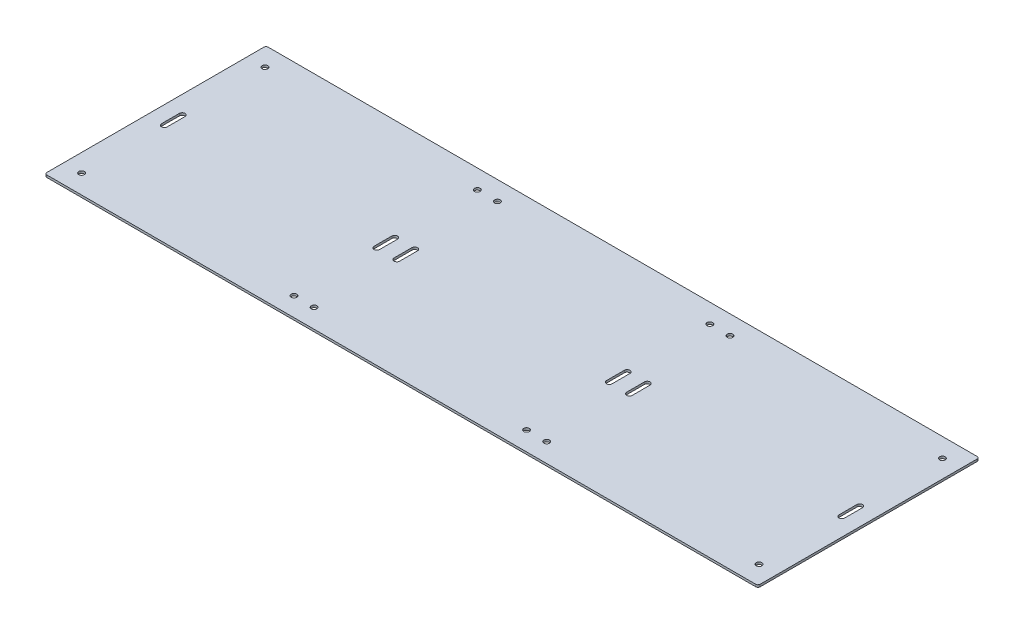
SolidWorks part; units mm, degrees
material "PC High Viscosity"
ref_plane "Front Plane" through (0, 0, 0) normal (0, 0, 1) x (1, 0, 0)
ref_plane "Top Plane" through (0, 0, 0) normal (0, 1, 0) x (1, 0, 0)
ref_plane "Right Plane" through (0, 0, 0) normal (1, 0, 0) x (0, 0, -1)
sketch "Sketch1" plane through (0, 0, 0) normal (0, 1, 0) x (1, 0, 0)
  line L0 (654.05, 574.675) -> (711.2, 574.675) construction
  line L1 (6.35, 0) -> (2019.3, 0)
  line L2 (0, 6.35) -> (0, 622.3)
  line L3 (6.35, 628.65) -> (2019.3, 628.65)
  line L4 (2025.65, 6.35) -> (2025.65, 622.3)
  line L5 (654.05, 574.675) -> (654.05, 53.975) construction
  line L6 (1371.6, 574.675) -> (1314.45, 574.675) construction
  line L7 (1371.6, 574.675) -> (1371.6, 53.975) construction
  line L8 (50.8, 339.725) -> (50.8, 288.925) construction
  line L9 (58.7375, 339.725) -> (58.7375, 288.925)
  line L10 (42.8625, 339.725) -> (42.8625, 288.925)
  line L11 (654.05, 339.725) -> (654.05, 288.925) construction
  line L12 (661.9875, 339.725) -> (661.9875, 288.925)
  line L13 (646.1125, 339.725) -> (646.1125, 288.925)
  line L14 (711.2, 339.725) -> (711.2, 288.925) construction
  line L15 (719.1375, 339.725) -> (719.1375, 288.925)
  line L16 (703.2625, 339.725) -> (703.2625, 288.925)
  line L17 (1012.825, 628.65) -> (1012.825, -49.4513) construction
  line L18 (1974.85, 339.725) -> (1974.85, 288.925) construction
  line L19 (1966.9125, 339.725) -> (1966.9125, 288.925)
  line L20 (1982.7875, 339.725) -> (1982.7875, 288.925)
  line L21 (1314.45, 339.725) -> (1314.45, 288.925) construction
  line L22 (1306.5125, 339.725) -> (1306.5125, 288.925)
  line L23 (1322.3875, 339.725) -> (1322.3875, 288.925)
  line L24 (1371.6, 339.725) -> (1371.6, 288.925) construction
  line L25 (1363.6625, 339.725) -> (1363.6625, 288.925)
  line L26 (1379.5375, 339.725) -> (1379.5375, 288.925)
  line L27 (50.8, 574.675) -> (0, 574.675) construction
  line L28 (1974.85, 574.675) -> (2025.65, 574.675) construction
  line L29 (1371.6, 53.975) -> (2025.65, 53.975) construction
  line L30 (654.05, 53.975) -> (0, 53.975) construction
  line L31 (50.8, 574.675) -> (50.8, 628.65) construction
  line L32 (50.8, 53.975) -> (50.8, 0) construction
  arc A0 (2019.3, 628.65) -> (2025.65, 622.3) centre (2019.3, 622.3) cw
  arc A1 (2019.3, 0) -> (2025.65, 6.35) centre (2019.3, 6.35) ccw
  arc A2 (6.35, 0) -> (0, 6.35) centre (6.35, 6.35) cw
  arc A3 (0, 622.3) -> (6.35, 628.65) centre (6.35, 622.3) cw
  circle A4 centre (50.8, 574.675) radius 7.9375
  circle A5 centre (1974.85, 574.675) radius 7.9375
  circle A6 centre (1974.85, 53.975) radius 7.9375
  circle A8 centre (50.8, 53.975) radius 7.9375
  circle A10 centre (654.05, 574.675) radius 7.9375
  circle A11 centre (1371.6, 574.675) radius 7.9375
  circle A12 centre (711.2, 574.675) radius 7.9375
  circle A13 centre (711.2, 53.975) radius 7.9375
  circle A15 centre (654.05, 53.975) radius 7.9375
  circle A17 centre (1314.45, 574.675) radius 7.9375
  circle A18 centre (1314.45, 53.975) radius 7.9375
  circle A20 centre (1371.6, 53.975) radius 7.9375
  arc A22 (58.7375, 339.725) -> (42.8625, 339.725) centre (50.8, 339.725) ccw
  arc A23 (42.8625, 288.925) -> (58.7375, 288.925) centre (50.8, 288.925) ccw
  arc A24 (661.9875, 339.725) -> (646.1125, 339.725) centre (654.05, 339.725) ccw
  arc A25 (646.1125, 288.925) -> (661.9875, 288.925) centre (654.05, 288.925) ccw
  arc A26 (719.1375, 339.725) -> (703.2625, 339.725) centre (711.2, 339.725) ccw
  arc A27 (703.2625, 288.925) -> (719.1375, 288.925) centre (711.2, 288.925) ccw
  arc A28 (1966.9125, 339.725) -> (1982.7875, 339.725) centre (1974.85, 339.725) cw
  arc A29 (1982.7875, 288.925) -> (1966.9125, 288.925) centre (1974.85, 288.925) cw
  arc A30 (1306.5125, 339.725) -> (1322.3875, 339.725) centre (1314.45, 339.725) cw
  arc A31 (1322.3875, 288.925) -> (1306.5125, 288.925) centre (1314.45, 288.925) cw
  arc A32 (1363.6625, 339.725) -> (1379.5375, 339.725) centre (1371.6, 339.725) cw
  arc A33 (1379.5375, 288.925) -> (1363.6625, 288.925) centre (1371.6, 288.925) cw
  point P7 (2025.65, 628.65)
  point P12 (0, 0)
  point P15 (0, 628.65)
  point P29 (50.8, 314.325)
  point P39 (711.2, 314.325)
  point P52 (654.05, 314.325)
  point P69 (1974.85, 314.325)
  point P76 (1314.45, 314.325)
  point P83 (1371.6, 314.325)
  point P89 (0, 314.325)
  dimension "D3" = 6.35
  dimension "D6" = 15.875
  dimension "D18" = 2
  dimension "D31" = 50.8
  dimension "D1" = 2025.65
  dimension "D2" = 628.65
  dimension "D4" = 50.8
  dimension "D5" = 53.975
  dimension "D9" = 654.05
  dimension "D20" = 57.15
  dimension "D21" = 57.15
  dimension "D25" = 90
  dimension "D26" = 57.15
  dimension "D28" = 50.8
  dimension "D7" = 2
  dimension "D8" = 2
  dimension "D19" = 2
  dimension "D23" = 2
  dimension "D24" = 2
  dimension "D29" = 2
extrude "Boss-Extrude1" add sketch "Sketch1" along normal blind 6.35
